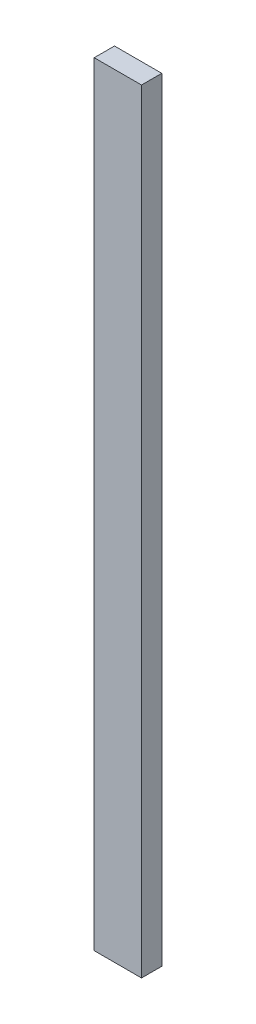
SolidWorks part; units mm, degrees
material "Oak"
ref_plane "Front Plane" through (0, 0, 0) normal (0, 0, 1) x (1, 0, 0)
ref_plane "Top Plane" through (0, 0, 0) normal (0, 1, 0) x (1, 0, 0)
ref_plane "Right Plane" through (0, 0, 0) normal (1, 0, 0) x (0, 0, -1)
sketch "Sketch1" plane through (0, 0, 0) normal (0, 1, 0) x (1, 0, 0)
  line L1 (-44.45, -19.05) -> (44.45, -19.05)
  line L2 (-44.45, -19.05) -> (-44.45, 19.05)
  line L3 (-44.45, 19.05) -> (44.45, 19.05)
  line L4 (44.45, -19.05) -> (44.45, 19.05)
  line L5 (-44.45, -19.05) -> (44.45, 19.05) construction
  line L6 (-44.45, 19.05) -> (44.45, -19.05) construction
  point P0 (0, 0)
  dimension "D1" = 38.1
  dimension "D2" = 88.9
extrude "Boss-Extrude1" add sketch "Sketch1" along normal blind 1454.15 contours L3 L4 L1 L2
